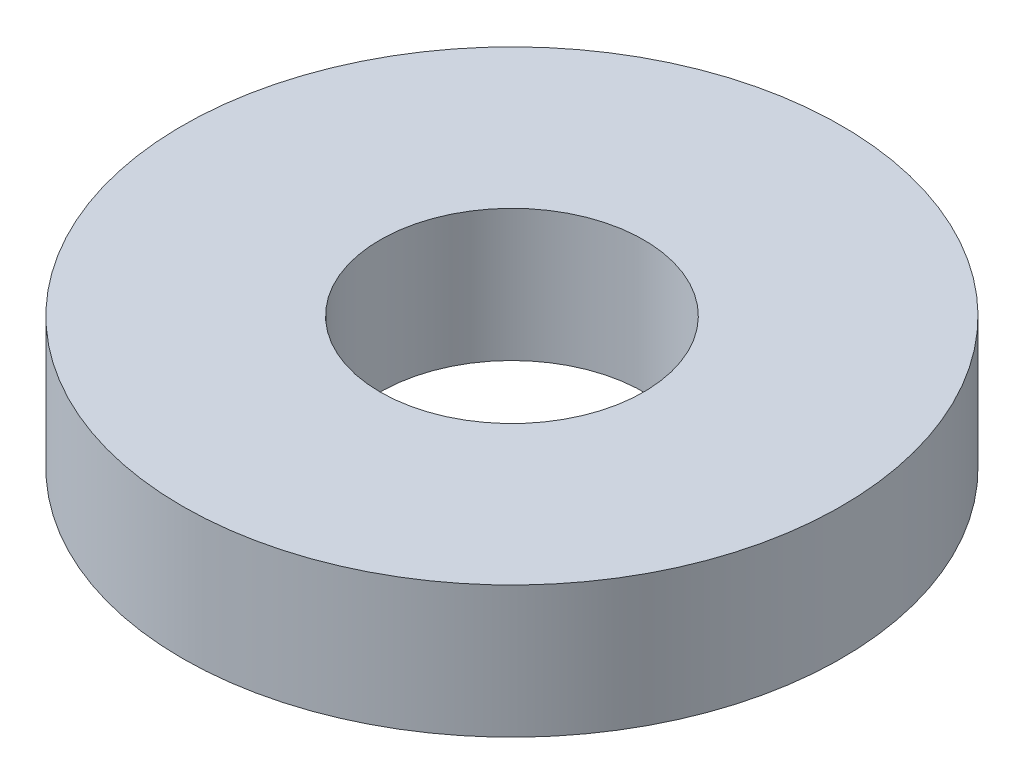
SolidWorks part; units mm, degrees
ref_plane "前视基准面" through (0, 0, 0) normal (0, 0, 1) x (1, 0, 0)
ref_plane "上视基准面" through (0, 0, 0) normal (0, 1, 0) x (1, 0, 0)
ref_plane "右视基准面" through (0, 0, 0) normal (1, 0, 0) x (0, 0, -1)
sketch "草图1" plane through (0, 0, 0) normal (0, 1, 0) x (1, 0, 0)
  circle A0 centre (0, 0) radius 2
  circle A1 centre (0, 0) radius 5
extrude "凸台-拉伸1" add sketch "草图1" along normal blind 2
